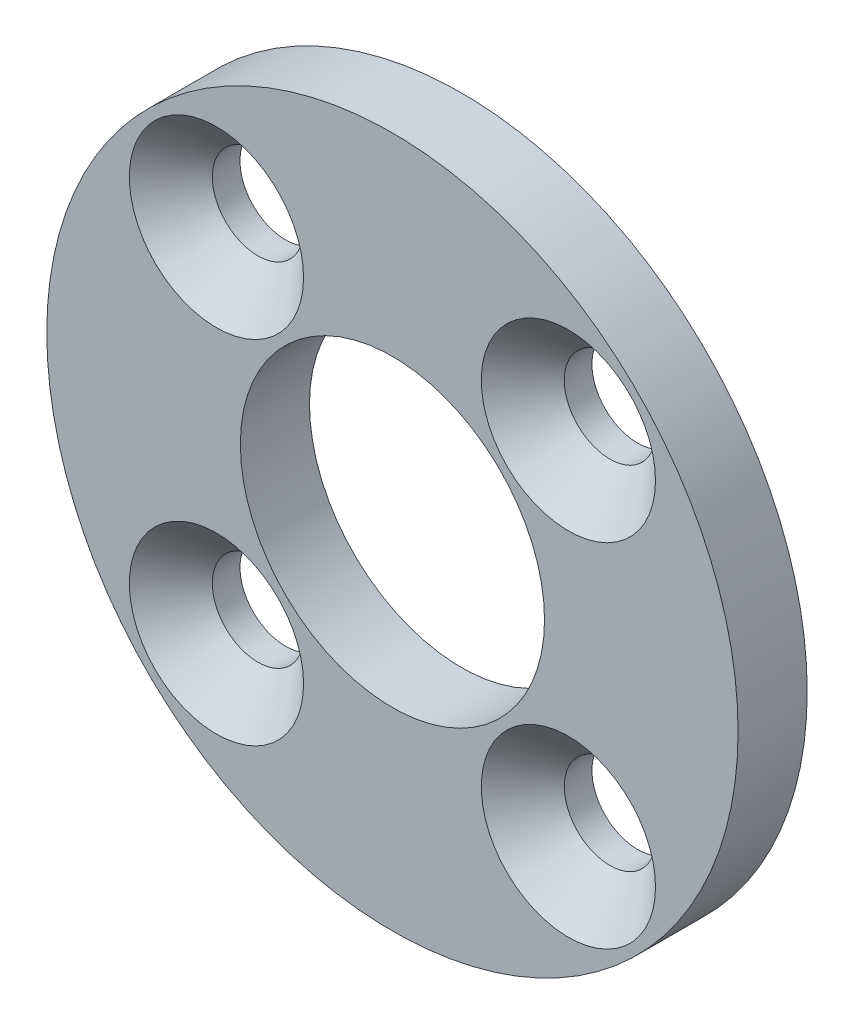
SolidWorks part; units mm, degrees
ref_plane "Plan de face" through (0, 0, 0) normal (0, 0, 1) x (1, 0, 0)
ref_plane "Plan de dessus" through (0, 0, 0) normal (0, 1, 0) x (1, 0, 0)
ref_plane "Plan de droite" through (0, 0, 0) normal (1, 0, 0) x (0, 0, -1)
sketch "Esquisse1" plane through (0, 0, 0) normal (0, 0, 1) x (1, 0, 0)
  circle A0 centre (0, 0) radius 25
  dimension "D1" = 50
extrude "Boss.-Extru.1" add sketch "Esquisse1" along normal blind 5
sketch "Esquisse2" plane through (0, 0, 5) normal (0, 0, 1) x (1, 0, 0)
  circle A0 centre (0, 0) radius 11
  dimension "D1" = 22
extrude "Enlèv. mat.-Extru.1" cut sketch "Esquisse2" against normal through all
hole_wizard "Fraisage pour vis à tête fraisée M61" positions "Esquisse7" profile "Esquisse8" countersink size "M6" standard "ISO" end condition through all
sketch "Esquisse7" plane through (0, 0, 5) normal (0, 0, 1) x (1, 0, 0)
  line L1 (-12.7279, -12.7279) -> (12.7279, -12.7279)
  line L2 (-12.7279, -12.7279) -> (-12.7279, 12.7279)
  line L3 (-12.7279, 12.7279) -> (12.7279, 12.7279)
  line L4 (12.7279, -12.7279) -> (12.7279, 12.7279)
  line L5 (-12.7279, -12.7279) -> (12.7279, 12.7279) construction
  line L6 (-12.7279, 12.7279) -> (12.7279, -12.7279) construction
  point P2 (12.7279, 12.7279)
  point P49 (-12.7279, -12.7279)
  point P50 (-12.7279, 12.7279)
  point P51 (12.7279, -12.7279)
  dimension "D1" = 36
sketch "Esquisse8" plane through (12.7279, 12.7279, 5) normal (1, 0, 0) x (0, -1, 0)
  line L0 (0, 0) -> (0, 5)
  line L1 (0, 5) -> (3.3, 5)
  line L2 (3.3, 5) -> (3.3, 3)
  line L3 (3.3, 3) -> (6.3, 0)
  line L5 (6.3, 0) -> (0, 0)
  line L6 (-3.3, 3) -> (-6.3, 0) construction
  line L11 (0, -6.35) -> (0, 107.95) construction
  dimension "Diamètre du perçage jusqu'au prochain" = 6.6
  dimension "Profondeur du perçage jusqu'au prochain" = 5
  dimension "Diamètre du fraisage entrant" = 12.6
  dimension "Angle du fraisage entrant" = 90
